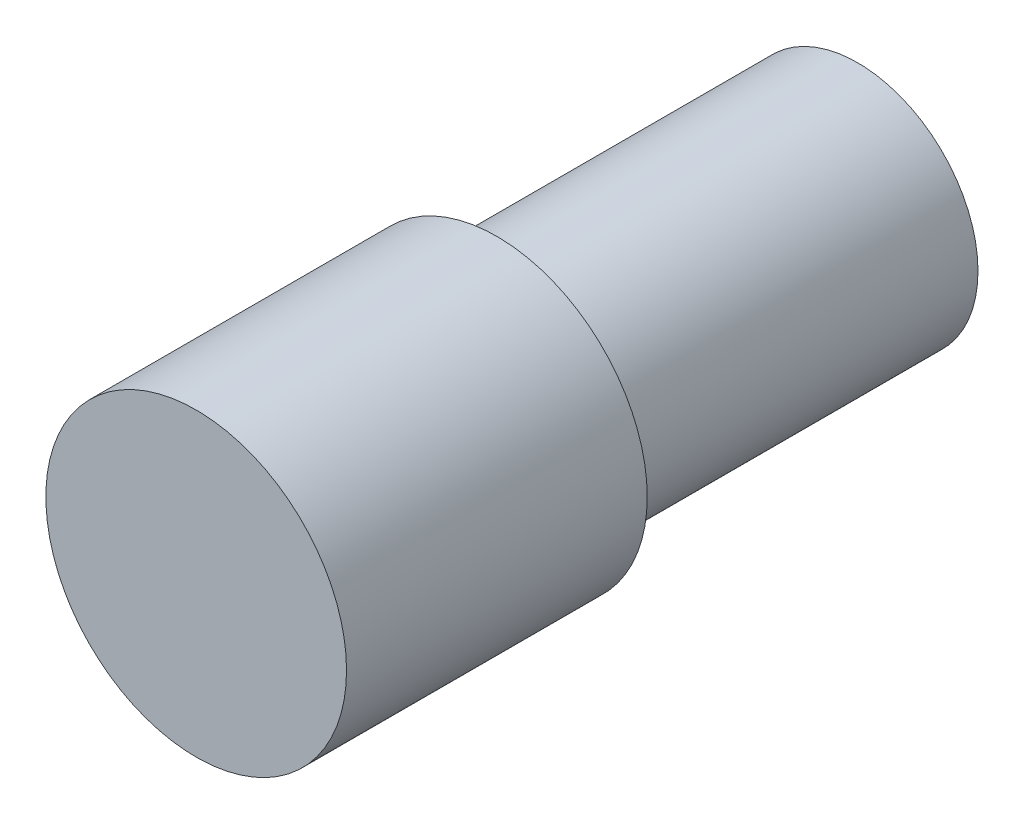
SolidWorks part; units mm, degrees
ref_plane "Plan de face" through (0, 0, 0) normal (0, 0, 1) x (1, 0, 0)
ref_plane "Plan de dessus" through (0, 0, 0) normal (0, 1, 0) x (1, 0, 0)
ref_plane "Plan de droite" through (0, 0, 0) normal (1, 0, 0) x (0, 0, -1)
sketch "Esquisse1" plane through (0, 0, 0) normal (0, 0, 1) x (1, 0, 0)
  circle A0 centre (0, 0) radius 5
  dimension "D1" = 10
extrude "Boss.-Extru.1" add sketch "Esquisse1" along normal blind 10
sketch "Esquisse2" plane through (0, 0, 0) normal (0, 0, -1) x (-1, 0, 0)
  circle A0 centre (0, 0) radius 4
  dimension "D1" = 8
extrude "Boss.-Extru.2" add sketch "Esquisse2" along normal blind 12
